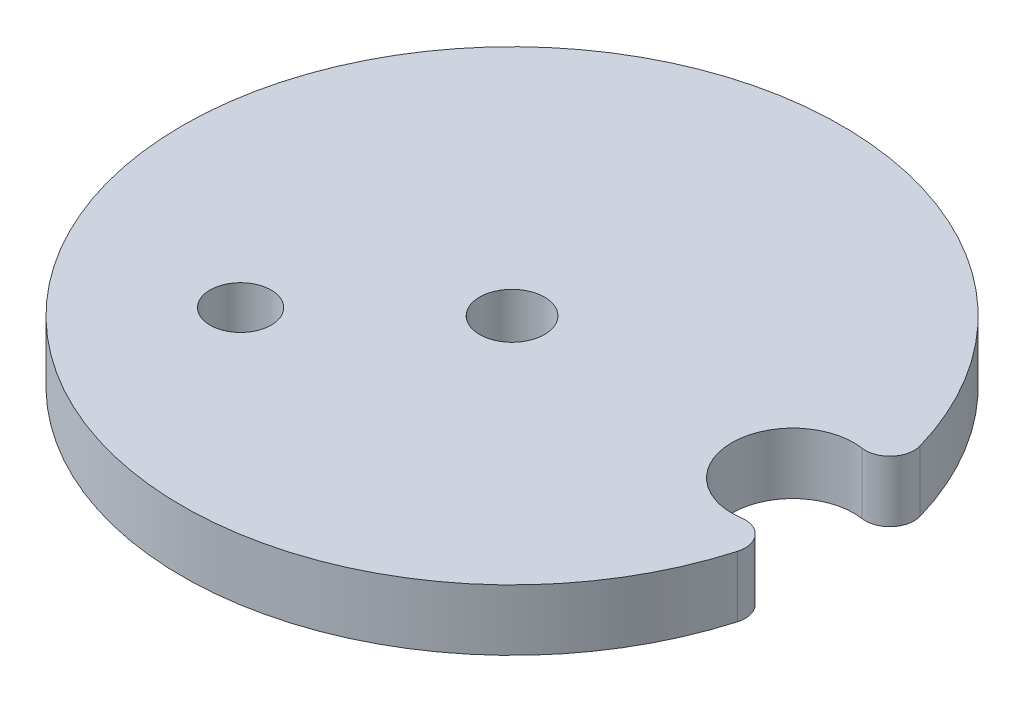
SolidWorks part; units mm, degrees
material "1023 Carbon Steel Sheet (SS)"
ref_plane "Front Plane" through (0, 0, 0) normal (0, 0, 1) x (1, 0, 0)
ref_plane "Top Plane" through (0, 0, 0) normal (0, 1, 0) x (1, 0, 0)
ref_plane "Right Plane" through (0, 0, 0) normal (1, 0, 0) x (0, 0, -1)
sketch "Sketch1" plane through (0, 0, 0) normal (0, 1, 0) x (1, 0, 0)
  circle A0 centre (0, 0) radius 34.29
  circle A1 centre (29.21, 0) radius 6.35
  dimension "D1" = 68.58
  dimension "D2" = 12.7
  dimension "D3" = 29.21
extrude "Boss-Extrude1" add sketch "Sketch1" along normal blind 6.35 contours A1 A0
hole_wizard "1/4 Clearance Hole1" positions "Sketch2" profile "Sketch3" hole size "1/4" standard "ANSI Inch" end condition through all
sketch "Sketch2" plane through (0, 6.35, 0) normal (0, 1, 0) x (1, 0, 0)
  point P0 (0, 0)
sketch "Sketch3" plane through (0, 6.35, 0) normal (1, 0, 0) x (0, 0, 1)
  line L0 (0, 0) -> (0, 6.35)
  line L1 (0, 6.35) -> (3.3782, 6.35)
  line L2 (3.3782, 6.35) -> (3.3782, 0)
  line L5 (3.3782, 0) -> (0, 0)
  line L11 (0, -6.35) -> (0, 107.95) construction
  dimension "Thru Hole Dia." = 6.7564
  dimension "Thru Hole Depth" = 6.35
fillet "Fillet1" radius 2.54 2 edges at (34.0415, 3.175, -4.1205) (34.0415, 3.175, 4.1205)
sketch "Sketch4" plane through (0, 6.35, 0) normal (0, 1, 0) x (1, 0, 0)
  line L0 (0, 0) -> (0, -34.29) construction
  line L1 (0, 0) -> (-14.8629, -13.3826) construction
  arc A0 (32.9482, 9.4984) -> (32.9482, -9.4984) centre (0, 0) ccw construction
  circle A1 centre (-14.8629, -13.3826) radius 3.175
  dimension "D3" = 6.35
  dimension "D1" = 48
  dimension "D2" = 20
extrude "Cut-Extrude1" cut sketch "Sketch4" against normal through all
